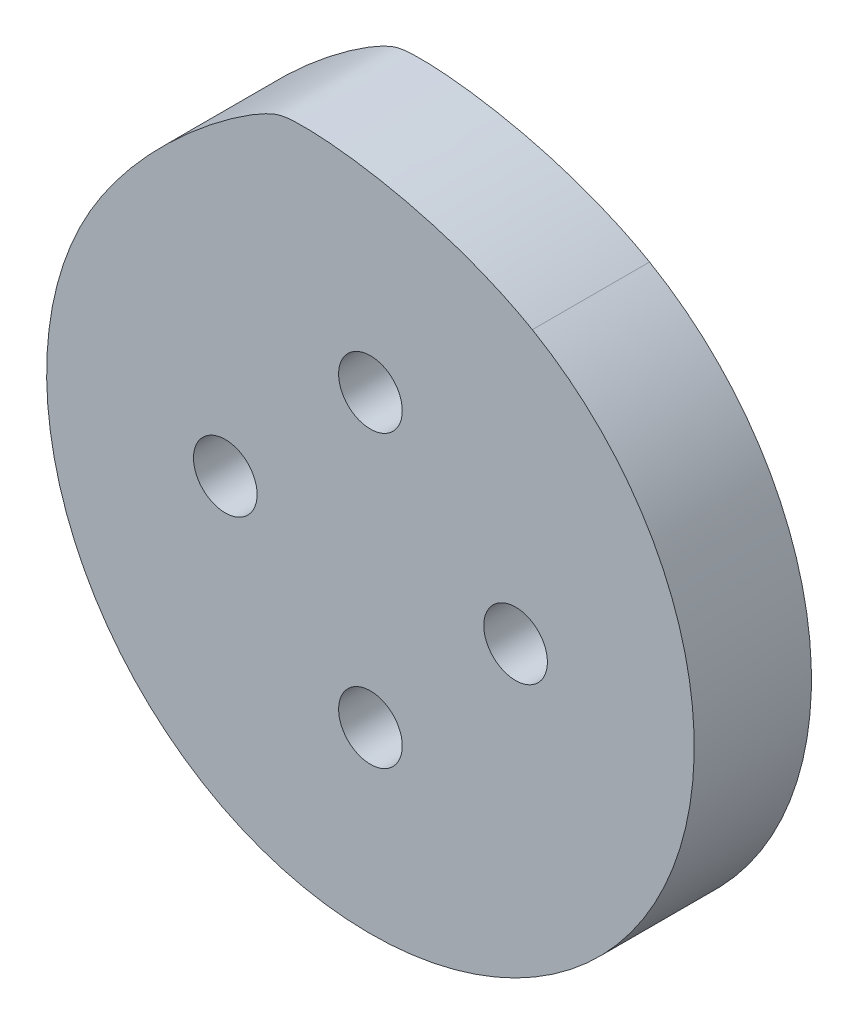
SolidWorks part; units mm, degrees
ref_plane "Front Plane" through (0, 0, 0) normal (1, 0, 0) x (0, 1, 0)
ref_plane "Top Plane" through (0, 0, 0) normal (0, 0, 1) x (0, 1, 0)
ref_plane "Right Plane" through (0, 0, 0) normal (0, 1, 0) x (-1, 0, 0)
sketch "Sketch1" plane through (0, 0, 0) normal (0, 0, 1) x (0, 1, 0)
  circle A0 centre (0, 0) radius 21
  circle A1 centre (0, 0) radius 13 construction
  circle A2 centre (0, 13) radius 1.6
  circle A3 centre (0, 13) radius 2.85
  circle A4 centre (13, 0) radius 2.85
  circle A5 centre (13, 0) radius 1.6
  circle A6 centre (0, -13) radius 2.85
  circle A7 centre (0, -13) radius 1.6
  circle A8 centre (-13, 0) radius 2.85
  circle A9 centre (-13, 0) radius 1.6
  point P19 (0, 0)
  dimension "D1" = 42
  dimension "D2" = 26
  dimension "D3" = 3.2
  dimension "D4" = 5.7
  dimension "D5" = 4
extrude "Boss-Extrude1" add sketch "Sketch1" along normal blind 10.5 contours A0 A8 A6 A4 A3 | A8 A9 | A3 A2 | A4 A5 | A6 A7
sketch "Sketch2" plane through (0, 0, 0) normal (0, 0, -1) x (1, 0, 0)
  line L0 (0, 0) -> (0, 31.5) construction
  line L1 (0, 0) -> (-8.1528, -30.4267) construction
  line L2 (0, 0) -> (-27.2798, -15.75) construction
  line L3 (0, 0) -> (15.75, -27.2798) construction
  line L4 (-9.9226, -29.9524) -> (-48.5597, -19.5997) construction
  line L5 (-4.4988, -50.2079) -> (-64.4988, 53.7152) construction
  line L6 (50.2079, -4.4988) -> (-53.7152, -64.4988) construction
  circle A0 centre (0, 0) radius 31.5 construction
  circle A1 centre (0, 0) radius 29
  spline S0 degree 3 poles (-25.1147, -14.5) (-20.6147, -22.2942) (-10.6927, -29.7861) (-5.6329, -31.1418) (6.7058, -29.6147) (14.5, -25.1147) knots 0 0 0 0 0.45 0.55 1 1 1 1
  circle M5 centre (0, 0) radius 21
  dimension "D1" = 63
  dimension "D2" = 58
  dimension "D6" = 20
  dimension "D7" = 30
  dimension "D8" = 30
  dimension "D3" = 195
  dimension "D4" = 45
  dimension "D5" = 45
  dimension "D9" = 90
  dimension "D10" = 90
  dimension "D11" = 90
extrude "Boss-Extrude3" add sketch "Sketch2" against normal up to surface (10.5 mm away) contours A1 M5 | A1 S0
sketch "Sketch3" plane through (0, 0, 0) normal (0, 0, -1) x (1, 0, 0)
  circle A0 centre (0, 0) radius 21
  circle A5 centre (-13, 0) radius 1.6
  circle A6 centre (0, 13) radius 1.6
  circle A7 centre (13, 0) radius 1.6
  circle A8 centre (0, -13) radius 1.6
  dimension "D1" = 42
extrude "Boss-Extrude4" add sketch "Sketch3" along normal blind 0.5
sketch "Sketch4" plane through (0, 0, 10.5) normal (0, 0, 1) x (1, 0, 0)
  circle A5 centre (-13, 0) radius 1.6
  circle A6 centre (0, 13) radius 1.6
  circle A7 centre (13, 0) radius 1.6
  circle A8 centre (0, -13) radius 1.6
  circle A9 centre (0, 13) radius 2.85
  circle A10 centre (13, 0) radius 2.85
  circle A11 centre (0, -13) radius 2.85
  circle A12 centre (-13, 0) radius 2.85
  dimension "D1" = 5.7
  dimension "D2" = 5.7
  dimension "D3" = 5.7
  dimension "D4" = 5.7
extrude "Cut-Extrude1" cut sketch "Sketch4" against normal blind 8.5 and the other way through all
